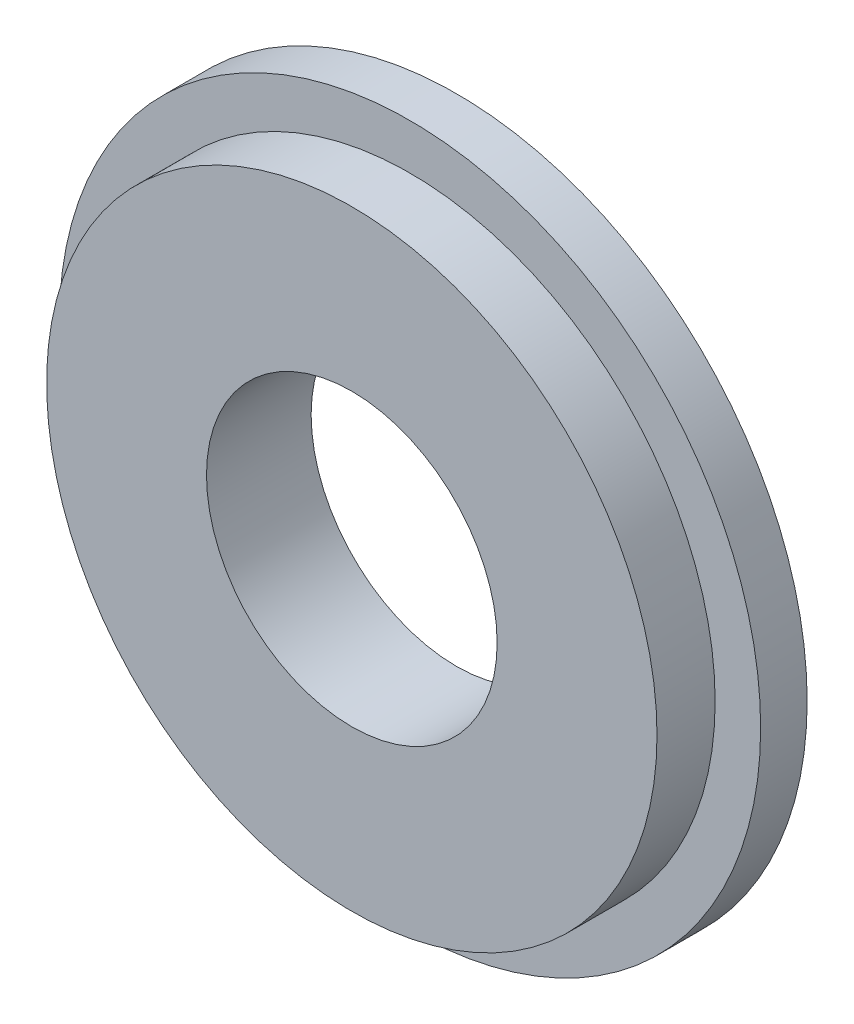
SolidWorks part; units mm, degrees
ref_plane "Front Plane" through (0, 0, 0) normal (0, 0, 1) x (1, 0, 0)
ref_plane "Top Plane" through (0, 0, 0) normal (0, 1, 0) x (1, 0, 0)
ref_plane "Right Plane" through (0, 0, 0) normal (1, 0, 0) x (0, 0, -1)
sketch "Sketch2" plane through (0, 0, 0) normal (0, 0, 1) x (1, 0, 0)
  circle A0 centre (0, 0) radius 30.165
  circle A1 centre (0, 0) radius 12.5
  dimension "D1" = 60.33
  dimension "D2" = 25
extrude "Boss-Extrude1" add sketch "Sketch2" along normal blind 4
sketch "Sketch3" plane through (0, 0, 4) normal (0, 0, 1) x (1, 0, 0)
  circle A0 centre (0, 0) radius 26.25
  circle A1 centre (0, 0) radius 12.5
  dimension "D1" = 52.5
  dimension "D2" = 25
extrude "Boss-Extrude2" add sketch "Sketch3" along normal blind 5
sketch "Croquis1" plane through (0, 0, 0) normal (0, 0, -1) x (-1, 0, 0)
  circle A0 centre (0, 0) radius 20 construction
  circle A1 centre (0, 20) radius 1.5
  circle A2 centre (0, -20) radius 1.6367
  circle A3 centre (20, 0) radius 1.5
  circle A4 centre (-20, 0) radius 1.5
  dimension "D1" = 40
  dimension "D2" = 3
  dimension "D3" = 3
  dimension "3" = 3.2734
  dimension "D4" = 3
extrude "Cortar-Extruir1" cut sketch "Croquis1" against normal blind 5
